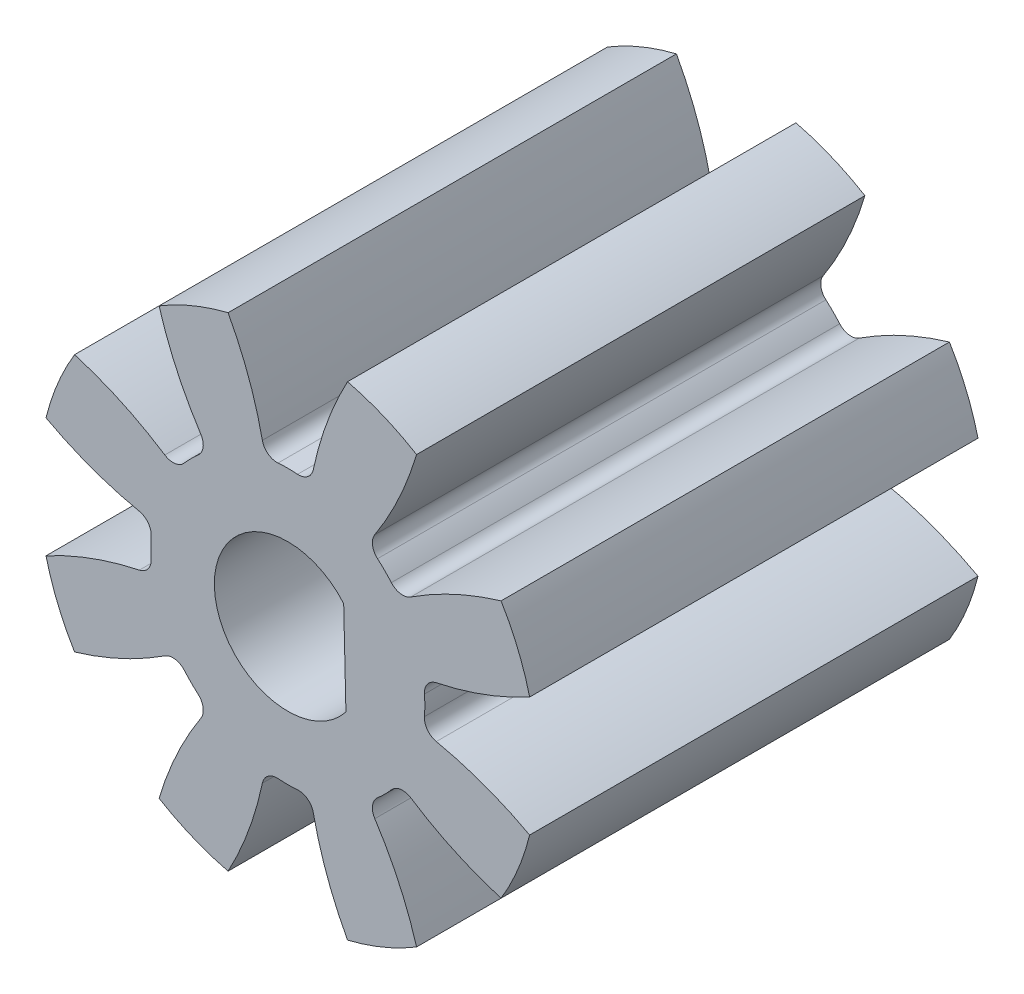
SolidWorks part; units mm, degrees
ref_plane "Alzado" through (0, 0, 0) normal (0, 0, 1) x (1, 0, 0)
ref_plane "Planta" through (0, 0, 0) normal (0, 1, 0) x (1, 0, 0)
ref_plane "Vista lateral" through (0, 0, 0) normal (1, 0, 0) x (0, 0, -1)
sketch "Croquis1" plane through (0, 0, 0) normal (0, 0, 1) x (1, 0, 0)
  circle A0 centre (0, 0) radius 8
  circle A1 centre (0, 0) radius 10
  circle A2 centre (0, 0) radius 5.5
  dimension "D1" = 16
  dimension "D2" = 20
  dimension "D3" = 4.5
extrude "Saliente-Extruir1" add sketch "Croquis1" along normal mid plane 18 contours A1
sketch "Croquis2" plane through (0, 0, 0) normal (0, 0, 1) x (1, 0, 0)
  line L0 (0, 0) -> (0, 10) construction
  line L1 (-1.5607, 7.8463) -> (1.5607, 7.8463) construction
  line L2 (-0.9197, 5.4226) -> (0, 0) construction
  line L3 (-2.5955, 10.6894) -> (0, 3.5582) construction
  line L4 (0, 0) -> (3.8268, 9.2388) construction
  line L5 (1.5607, 7.8463) -> (4.4446, 6.6518) construction
  circle A0 centre (0, 0) radius 10 construction
  arc A3 (-0.9197, 5.4226) -> (-2.9275, 10.6033) centre (-14.5907, 3.1038) ccw
  arc A4 (0.9197, 5.4226) -> (2.9275, 10.6033) centre (14.5907, 3.1038) cw
  circle A5 centre (0, 0) radius 5.5 construction
  arc A7 (0.9197, 5.4226) -> (-0.9197, 5.4226) centre (0, 0) ccw
  circle A9 centre (0, 0) radius 8 construction
  circle A10 centre (0, 0) radius 11
  arc A11 (2.9275, 10.6033) -> (-2.9275, 10.6033) centre (0, 0) ccw
  dimension "D2" = 20
  dimension "D3" = 22.5
  dimension "D1" = 1
extrude "Cortar-Extruir1" cut sketch "Croquis2" against normal through all and the other way through all
fillet "Redondeo1" radius 0.6 2 edges at (0.9197, 5.4226, 0) (-0.9197, 5.4226, 0)
pattern_circular "MatrizC1" count 8 over 360 about axis through (0, 0, 0) along (0, 0, 1) of "Redondeo1", "Cortar-Extruir1"
sketch "Croquis3" plane through (0, 0, 0) normal (0, 0, 1) x (1, 0, 0)
  line L0 (2.2429, 1.9162) -> (2.3327, -1.8058)
  arc A1 (2.2429, 1.9162) -> (2.3327, -1.8058) centre (0, 0) ccw
  dimension "D1" = 5.9
extrude "Cortar-Extruir2" cut sketch "Croquis3" against normal up to surface (18 mm away) from surface at 9 up to face at (0, 0, -9) starting at face at (0, 0, 9)
equation "\"Modulo\"= 2mm"
equation "\"Numero de Dientes\"= 8"
equation "\"D1@Croquis1\"=\"Modulo\"*\"Numero de Dientes\""
equation "\"D2@Croquis1\"=(\"Numero de Dientes\"+2)*\"Modulo\""
equation "\"D3@Croquis1\"=\"Modulo\"*if( \"Modulo\" =>1.25,2.25,2.4)"
equation "\"D3@Croquis2\"=180/\"Numero de Dientes\""
equation "\"D1@Redondeo1\"=.3*\"Modulo\""
equation "\"D1@MatrizC1\"=\"Numero de Dientes\""
